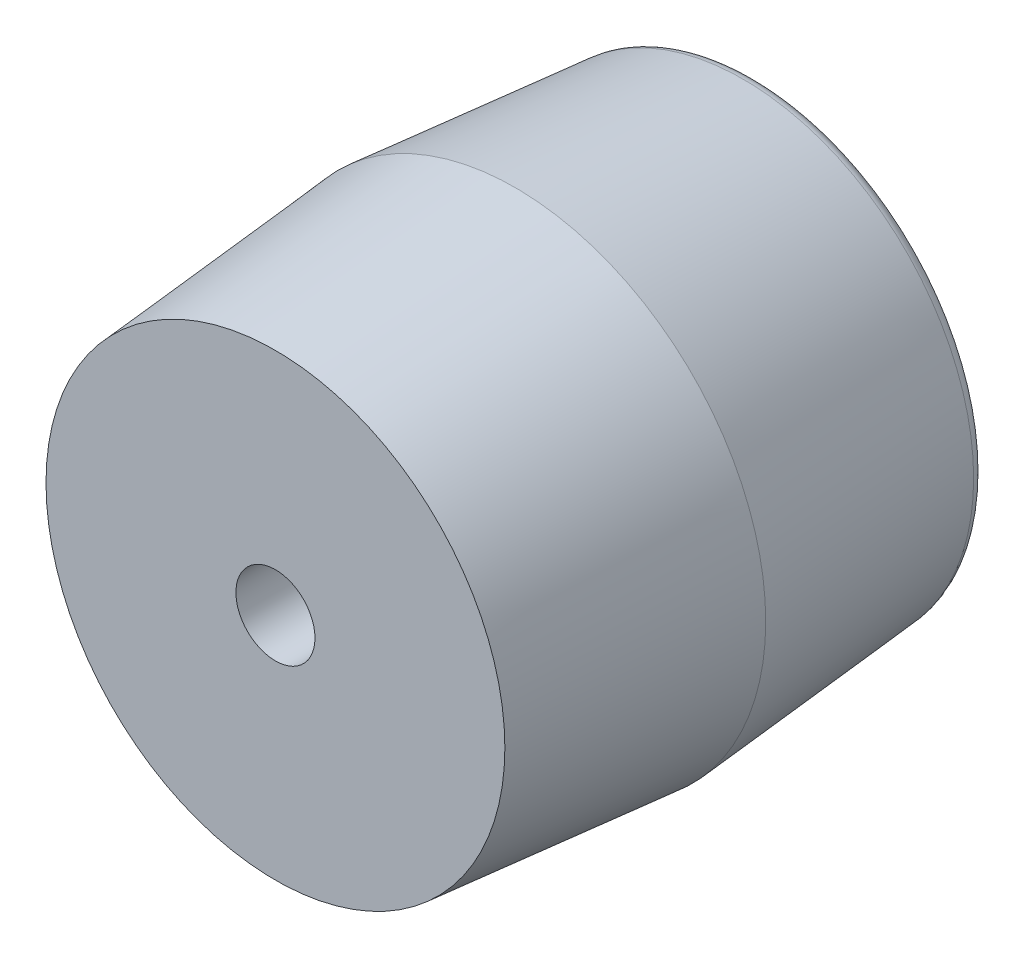
SolidWorks part; units mm, degrees
other "攝影機1"
material "BUTYL"
ref_plane "Front Plane" through (0, 0, 0) normal (0, 0, 1) x (1, 0, 0)
ref_plane "Top Plane" through (0, 0, 0) normal (0, 1, 0) x (1, 0, 0)
ref_plane "Right Plane" through (0, 0, 0) normal (1, 0, 0) x (0, 0, -1)
sketch "Sketch1" plane through (0, 0, 0) normal (0, 0, 1) x (1, 0, 0)
  circle A0 centre (0, 0) radius 9.5
  dimension "D1" = 19
extrude "Boss-Extrude1" add sketch "Sketch1" along normal mid plane 18.2 draft 5
fillet "Fillet1" radius 0.5 1 edges at (8.7039, 0, -9.1)
sketch "Sketch2" plane through (0, 0, 9.1) normal (0, 0, 1) x (1, 0, 0)
  circle A0 centre (0, 0) radius 1.5
extrude "Cut-Extrude1" cut sketch "Sketch2" against normal blind 18.5
